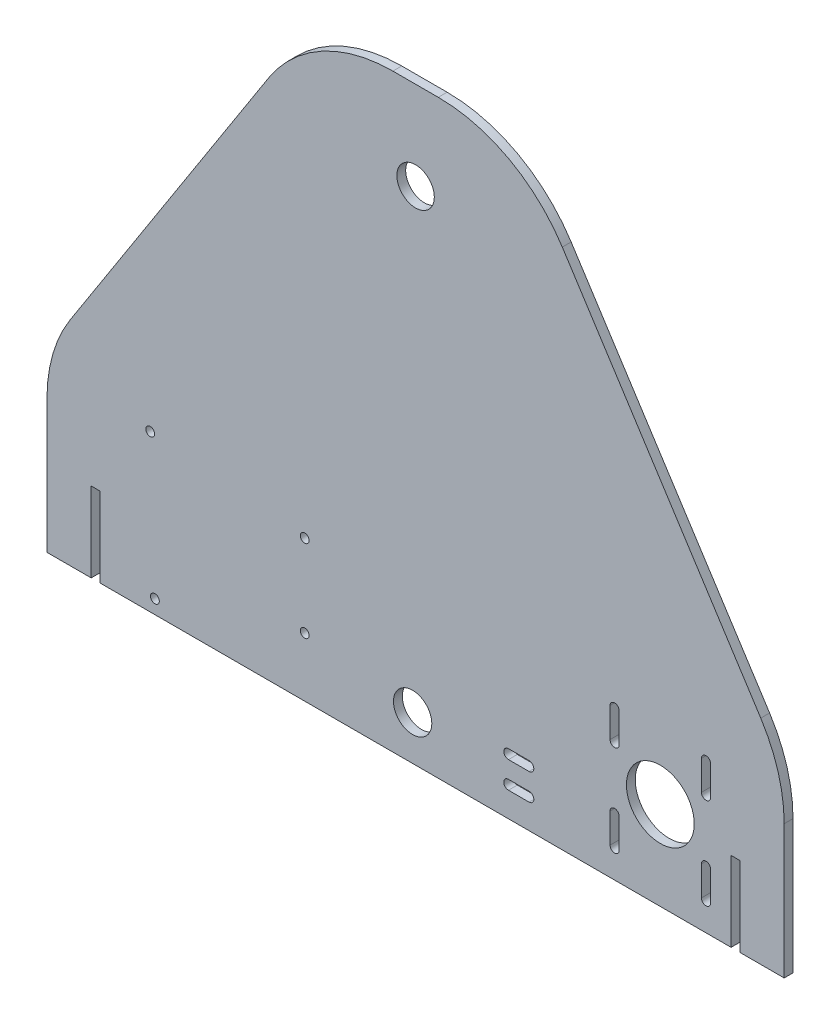
SolidWorks part; units mm, degrees
ref_plane "Alzado" through (0, 0, 0) normal (0, 0, 1) x (1, 0, 0)
ref_plane "Planta" through (0, 0, 0) normal (0, 1, 0) x (1, 0, 0)
ref_plane "Vista lateral" through (0, 0, 0) normal (1, 0, 0) x (0, 0, -1)
sketch "Croquis1" plane through (0, 0, 0) normal (0, 0, 1) x (1, 0, 0)
  line L0 (-125, -40) -> (-35, 100)
  line L1 (-125, 100) -> (125, 100)
  line L2 (-125, 100) -> (-125, -100)
  line L3 (-125, -100) -> (125, -100)
  line L4 (125, 100) -> (125, -100)
  line L5 (-125, 100) -> (125, -100) construction
  line L6 (-125, -100) -> (125, 100) construction
  line L7 (35, 100) -> (125, -40)
  circle A0 centre (0, 70) radius 6.35
  point P0 (0, 0)
  dimension "D7" = 12.7
  dimension "D1" = 250
  dimension "D2" = 200
  dimension "D3" = 60
  dimension "D4" = 60
  dimension "D5" = 90
  dimension "D6" = 90
  dimension "D8" = 35
  dimension "D9" = 30
extrude "Saliente-Extruir1" add sketch "Croquis1" along normal blind 3 contours L7 L1 L0 L2 L3 L4 A0
fillet "Redondeo1" radius 50 4 edges at (125, -40, 1.5) (-125, -40, 1.5) (35, 100, 1.5) (-35, 100, 1.5)
sketch "Croquis2" plane through (0, 0, 3) normal (0, 0, 1) x (1, 0, 0)
  line L0 (125, -54.6851) -> (125, -100) construction
  line L1 (67.5, -54.5) -> (98.5, -54.5)
  line L2 (67.5, -54.5) -> (67.5, -85.5)
  line L3 (67.5, -85.5) -> (98.5, -85.5)
  line L4 (98.5, -54.5) -> (98.5, -85.5)
  line L5 (67.5, -54.5) -> (98.5, -85.5) construction
  line L6 (67.5, -85.5) -> (98.5, -54.5) construction
  line L7 (-125, -100) -> (125, -100) construction
  circle A0 centre (67.5, -54.5) radius 1.5
  circle A1 centre (98.5, -54.5) radius 1.5
  circle A2 centre (98.5, -85.5) radius 1.5
  circle A3 centre (67.5, -85.5) radius 1.5
  circle A4 centre (83, -70) radius 11.5
  point P0 (83, -70)
  dimension "D5" = 3
  dimension "D6" = 3
  dimension "D7" = 3
  dimension "D8" = 3
  dimension "D9" = 23
  dimension "D1" = 31
  dimension "D2" = 31
  dimension "D3" = 42
  dimension "D4" = 30
extrude "Cortar-Extruir1" cut sketch "Croquis2" against normal blind 10 contours L4 A1 L1 | L1 A1 L4 | L1 A0 L2 | L2 A0 L1 | A4 | L2 A3 L3 | L3 A3 L2 | L3 A2 L4 | L4 A2 L3
sketch "Croquis3" plane through (0, 0, 3) normal (0, 0, 1) x (1, 0, 0)
sketch "Croquis6" plane through (0, 0, 0) normal (0, 0, -1) x (-1, 0, 0)
  line L0 (125, -100) -> (-125, -100) construction
  line L1 (-110, -100) -> (-107, -100)
  line L2 (-110, -100) -> (-110, -73)
  line L3 (-110, -73) -> (-107, -73)
  line L4 (-107, -100) -> (-107, -73)
  line L5 (-125, -54.6851) -> (-125, -100) construction
  line L6 (125, -54.6851) -> (125, -100) construction
  line L7 (110, -100) -> (107, -100)
  line L8 (110, -100) -> (110, -73)
  line L9 (110, -73) -> (107, -73)
  line L10 (107, -100) -> (107, -73)
  dimension "D1" = 27
  dimension "D2" = 3
  dimension "D3" = 15
  dimension "D4" = 27
  dimension "D5" = 3
  dimension "D6" = 15
extrude "Cortar-Extruir3" cut sketch "Croquis6" against normal through all
sketch "Croquis7" plane through (0, 0, 0) normal (0, 0, -1) x (-1, 0, 0)
  line L0 (107, -100) -> (-107, -100) construction
  line L1 (125, -54.6851) -> (125, -100) construction
  circle A0 centre (90, -47) radius 1.5
  circle A1 centre (37.6, -52.1) radius 1.5
  circle A2 centre (37.6, -80) radius 1.5
  circle A3 centre (88.4, -95.3) radius 1.5
  dimension "D1" = 3
  dimension "D2" = 3
  dimension "D3" = 3
  dimension "D4" = 3
  dimension "D5" = 52.4
  dimension "D6" = 27.9
  dimension "D7" = 0
  dimension "D8" = 33
  dimension "D9" = 50.8
  dimension "D10" = 48.3
  dimension "D11" = 53
  dimension "D12" = 35
extrude "Cortar-Extruir4" cut sketch "Croquis7" against normal through all
sketch "Croquis8" plane through (0, 0, 3) normal (0, 0, 1) x (1, 0, 0)
  line L0 (31.5, -90) -> (38.5, -90) construction
  line L2 (-125, -54.6851) -> (-125, -100) construction
  line L4 (31.5, -88.4) -> (38.5, -88.4)
  line L5 (31.5, -91.6) -> (38.5, -91.6)
  line L6 (31.5, -81) -> (38.5, -81) construction
  line L7 (31.5, -79.4) -> (38.5, -79.4)
  line L8 (31.5, -82.6) -> (38.5, -82.6)
  line L9 (-107, -100) -> (107, -100) construction
  line L10 (125, -54.6851) -> (125, -100) construction
  circle A2 centre (-1, -85) radius 6.5
  arc A3 (31.5, -88.4) -> (31.5, -91.6) centre (31.5, -90) ccw
  arc A4 (38.5, -91.6) -> (38.5, -88.4) centre (38.5, -90) ccw
  arc A5 (31.5, -79.4) -> (31.5, -82.6) centre (31.5, -81) ccw
  arc A6 (38.5, -82.6) -> (38.5, -79.4) centre (38.5, -81) ccw
  point P17 (35, -90)
  point P24 (35, -81)
  dimension "D1" = 13
  dimension "D3" = 1.6
  dimension "D5" = 1.6
  dimension "D2" = 7
  dimension "D4" = 7
  dimension "D6" = 10
  dimension "D7" = 9
  dimension "D8" = 90
  dimension "D9" = 90
  dimension "D10" = 15
  dimension "D11" = 124
extrude "Cortar-Extruir5" cut sketch "Croquis8" against normal through all
sketch "Croquis9" plane through (0, 0, 0) normal (0, 0, -1) x (-1, 0, 0)
  line L0 (-98.5, -49.5) -> (-98.5, -59.5) construction
  line L1 (-96.95, -49.5) -> (-96.95, -59.5)
  line L2 (-100.05, -49.5) -> (-100.05, -59.5)
  line L3 (-67.5, -49.5) -> (-67.5, -59.5) construction
  line L4 (-65.95, -49.5) -> (-65.95, -59.5)
  line L5 (-69.05, -49.5) -> (-69.05, -59.5)
  line L6 (-67.5, -90.5) -> (-67.5, -80.5) construction
  line L7 (-69.05, -90.5) -> (-69.05, -80.5)
  line L8 (-65.95, -90.5) -> (-65.95, -80.5)
  line L9 (-98.5, -90.5) -> (-98.5, -80.5) construction
  line L10 (-100.05, -90.5) -> (-100.05, -80.5)
  line L11 (-96.95, -90.5) -> (-96.95, -80.5)
  arc A0 (-96.95, -49.5) -> (-100.05, -49.5) centre (-98.5, -49.5) ccw
  arc A1 (-100.05, -59.5) -> (-96.95, -59.5) centre (-98.5, -59.5) ccw
  arc A2 (-65.95, -49.5) -> (-69.05, -49.5) centre (-67.5, -49.5) ccw
  arc A3 (-69.05, -59.5) -> (-65.95, -59.5) centre (-67.5, -59.5) ccw
  arc A4 (-69.05, -90.5) -> (-65.95, -90.5) centre (-67.5, -90.5) ccw
  arc A5 (-65.95, -80.5) -> (-69.05, -80.5) centre (-67.5, -80.5) ccw
  arc A6 (-100.05, -90.5) -> (-96.95, -90.5) centre (-98.5, -90.5) ccw
  arc A7 (-96.95, -80.5) -> (-100.05, -80.5) centre (-98.5, -80.5) ccw
  point P2 (-98.5, -54.5)
  point P9 (-67.5, -54.5)
  point P17 (-67.5, -85.5)
  point P25 (-98.5, -85.5)
  dimension "D1" = 1.55
  dimension "D2" = 1.55
  dimension "D3" = 1.55
  dimension "D4" = 1.55
  dimension "D5" = 10
  dimension "D6" = 10
  dimension "D7" = 10
  dimension "D8" = 10
extrude "Cortar-Extruir6" cut sketch "Croquis9" against normal through all
